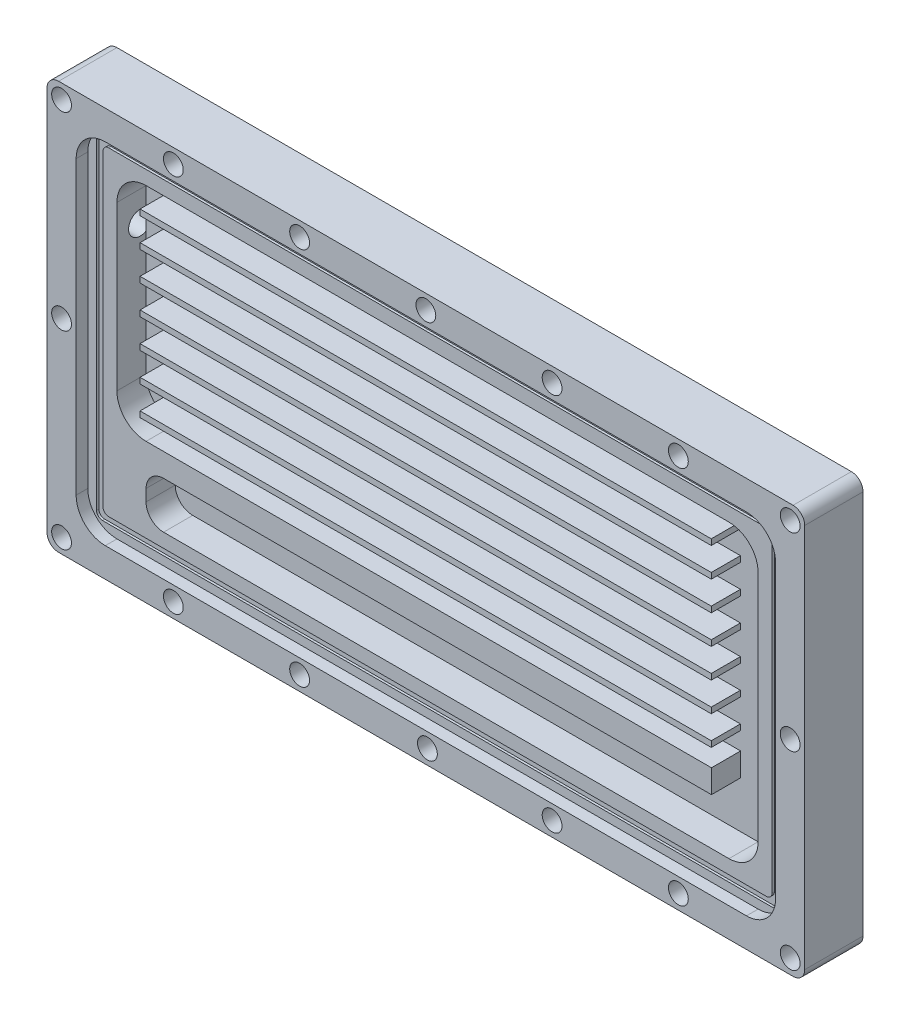
SolidWorks part; units mm, degrees
ref_plane "Plan de face" through (0, 0, 0) normal (0, 0, 1) x (1, 0, 0)
ref_plane "Plan de dessus" through (0, 0, 0) normal (0, 1, 0) x (1, 0, 0)
ref_plane "Plan de droite" through (0, 0, 0) normal (1, 0, 0) x (0, 0, -1)
sketch "Esquisse1" plane through (0, 0, 0) normal (0, 0, 1) x (1, 0, 0)
  line L1 (2, 0) -> (128, 0)
  line L2 (0, 2) -> (0, 68)
  line L3 (2, 70) -> (128, 70)
  line L4 (130, 2) -> (130, 68)
  arc A0 (2, 0) -> (0, 2) centre (2, 2) cw
  arc A1 (128, 0) -> (130, 2) centre (128, 2) ccw
  arc A2 (128, 70) -> (130, 68) centre (128, 68) cw
  arc A3 (0, 68) -> (2, 70) centre (2, 68) cw
  point P7 (0, 0)
  point P10 (130, 0)
  point P15 (0, 70)
  dimension "D3" = 2
  dimension "D1" = 130
  dimension "D2" = 70
extrude "Boss.-Extru.1" add sketch "Esquisse1" along normal blind 10
sketch "Esquisse18" plane through (0, 0, 10) normal (0, 0, 1) x (1, 0, 0)
  line L0 (128, 70) -> (2, 70) construction
  line L1 (10, 5) -> (120, 5)
  line L2 (5, 10) -> (5, 60)
  line L3 (10, 65) -> (120, 65)
  line L4 (125, 10) -> (125, 60)
  line L5 (130, 2) -> (130, 68) construction
  line L6 (0, 68) -> (0, 2) construction
  line L7 (2, 0) -> (128, 0) construction
  arc A0 (120, 65) -> (125, 60) centre (120, 60) cw
  arc A1 (120, 5) -> (125, 10) centre (120, 10) ccw
  arc A2 (10, 5) -> (5, 10) centre (10, 10) cw
  arc A3 (5, 60) -> (10, 65) centre (10, 60) cw
  dimension "D5" = 5
  dimension "D1" = 5
  dimension "D2" = 5
  dimension "D3" = 5
  dimension "D4" = 5
extrude "Enlèv. mat.-Extru.1" cut sketch "Esquisse18" against normal blind 2
sketch "Esquisse19" plane through (0, 0, 0) normal (-1, 0, 0) x (0, 0, 1)
  circle A0 centre (4, 50) radius 2
  circle A1 centre (4, 12) radius 2
sketch "Esquisse20" plane through (0, 0, 8) normal (0, 0, 1) x (1, 0, 0)
  line L0 (15, 60) -> (115, 60)
  line L9 (120, 55) -> (120, 15)
  line L10 (115, 10) -> (18, 10)
  line L12 (18, 18) -> (112, 18)
  line L14 (112, 22) -> (15, 22)
  line L25 (112, 18) -> (112, 22)
  line L26 (10, 27) -> (10, 55)
  line L28 (15, 13) -> (15, 15)
  line L32 (5, 60) -> (5, 10) construction
  line L33 (5, 60) -> (5, 10) construction
  line L34 (10, 5) -> (120, 5) construction
  line L35 (125, 10) -> (125, 60) construction
  line L36 (120, 65) -> (10, 65) construction
  arc A0 (15, 22) -> (10, 27) centre (15, 27) cw
  arc A1 (10, 55) -> (15, 60) centre (15, 55) cw
  arc A2 (120, 15) -> (115, 10) centre (115, 15) cw
  arc A3 (115, 60) -> (120, 55) centre (115, 55) cw
  arc A4 (15, 15) -> (18, 18) centre (18, 15) cw
  arc A5 (18, 10) -> (15, 13) centre (18, 13) cw
  dimension "D10" = 5
  dimension "D9" = 3
  dimension "D11" = 3
  dimension "D2" = 5
  dimension "D3" = 10
  dimension "D4" = 8
  dimension "D5" = 8
  dimension "D6" = 5
  dimension "D7" = 5
  dimension "D8" = 5
  dimension "D14" = 4
extrude "Enlèv. mat.-Extru.3" cut sketch "Esquisse20" against normal blind 5
sketch "Esquisse23" plane through (0, 0, 3) normal (0, 0, 1) x (1, 0, 0)
  line L1 (13.9661, 56) -> (111.9661, 56)
  line L2 (13.9661, 56) -> (13.9661, 55)
  line L3 (13.9661, 55) -> (111.9661, 55)
  line L4 (111.9661, 56) -> (111.9661, 55)
  line L28 (115, 60) -> (15, 60) construction
  line L29 (13.9661, 51) -> (111.9661, 51)
  line L30 (13.9661, 50) -> (111.9661, 50)
  line L31 (111.9661, 51) -> (111.9661, 50)
  line L32 (13.9661, 51) -> (13.9661, 50)
  line L33 (13.9661, 46) -> (111.9661, 46)
  line L34 (13.9661, 45) -> (111.9661, 45)
  line L35 (111.9661, 46) -> (111.9661, 45)
  line L36 (13.9661, 46) -> (13.9661, 45)
  line L37 (13.9661, 41) -> (111.9661, 41)
  line L38 (13.9661, 40) -> (111.9661, 40)
  line L39 (111.9661, 41) -> (111.9661, 40)
  line L40 (13.9661, 41) -> (13.9661, 40)
  line L41 (13.9661, 36) -> (111.9661, 36)
  line L42 (13.9661, 35) -> (111.9661, 35)
  line L43 (111.9661, 36) -> (111.9661, 35)
  line L44 (13.9661, 36) -> (13.9661, 35)
  line L45 (13.9661, 31) -> (111.9661, 31)
  line L46 (13.9661, 30) -> (111.9661, 30)
  line L47 (111.9661, 31) -> (111.9661, 30)
  line L48 (13.9661, 31) -> (13.9661, 30)
  line L49 (13.9661, 26) -> (111.9661, 26)
  line L50 (13.9661, 25) -> (111.9661, 25)
  line L51 (111.9661, 26) -> (111.9661, 25)
  line L52 (13.9661, 26) -> (13.9661, 25)
  dimension "D1" = 98
  dimension "D2" = 7
  dimension "D3" = 1
  dimension "D4" = 4
extrude "Boss.-Extru.2" add sketch "Esquisse23" along normal blind 5
sketch "Esquisse24" plane through (0, 0, 8) normal (0, 0, 1) x (1, 0, 0)
  line L0 (8.6, 62.4) -> (121.4, 62.4)
  line L2 (6.5, 62.5) -> (6.5, 7.5)
  line L3 (7.5, 6.5) -> (7.9673, 6.5)
  line L5 (7.9673, 6.5) -> (122.5, 6.5)
  line L10 (123.5, 7.5) -> (123.5, 62.5)
  line L12 (122.4, 8.6) -> (122.4, 61.4)
  line L15 (122.5, 63.5) -> (7.5, 63.5)
  line L17 (121.4, 7.6) -> (8.6, 7.6)
  line L18 (7.6, 8.6) -> (7.6, 61.4)
  line L19 (5, 60) -> (5, 10) construction
  line L20 (120, 65) -> (10, 65) construction
  line L21 (125, 10) -> (125, 60) construction
  line L22 (10, 5) -> (120, 5) construction
  arc A0 (121.4, 7.6) -> (122.4, 8.6) centre (121.4, 8.6) ccw
  arc A1 (122.5, 6.5) -> (123.5, 7.5) centre (122.5, 7.5) ccw
  arc A2 (123.5, 62.5) -> (122.5, 63.5) centre (122.5, 62.5) ccw
  arc A3 (121.4, 62.4) -> (122.4, 61.4) centre (121.4, 61.4) cw
  arc A4 (8.6, 62.4) -> (7.6, 61.4) centre (8.6, 61.4) ccw
  arc A5 (7.5, 63.5) -> (6.5, 62.5) centre (7.5, 62.5) ccw
  arc A6 (6.5, 7.5) -> (7.5, 6.5) centre (7.5, 7.5) ccw
  arc A7 (8.6, 7.6) -> (7.6, 8.6) centre (8.6, 8.6) cw
  dimension "D9" = 1
  dimension "D1" = 1.1
  dimension "D2" = 1.1
  dimension "D3" = 1.5
  dimension "D4" = 1.5
  dimension "D5" = 1.5
  dimension "D6" = 1.1
  dimension "D7" = 1.1
  dimension "D8" = 1.5
extrude "Enlèv. mat.-Extru.4" cut sketch "Esquisse24" against normal blind 0.4
extrude "Enlèv. mat.-Extru.5" cut sketch "Esquisse19" against normal blind 10
sketch "Esquisse25" plane through (0, 0, 10) normal (0, 0, 1) x (1, 0, 0)
  line L0 (65, 76.2778) -> (65, -9.8597) construction
  line L1 (86.66, 74.4744) -> (86.66, -13.393) construction
  line L2 (108.32, 74.4744) -> (108.32, -15.3804) construction
  line L3 (43.34, 74.4744) -> (43.34, -9.8597) construction
  line L4 (21.68, 74.4744) -> (21.68, -9.8597) construction
  line L5 (-6.6333, 67.5) -> (135.9663, 67.5) construction
  line L6 (-6.6333, 35) -> (142.1485, 35) construction
  line L7 (2, 0) -> (128, 0) construction
  line L8 (-6.6333, 2.5) -> (137.1669, 2.5) construction
  line L9 (130, 2) -> (130, 68) construction
  line L10 (128, 70) -> (2, 70) construction
  line L11 (2.5, 74.4744) -> (2.5, -9.8597) construction
  line L12 (127.5, 74.4744) -> (127.5, -3.6286) construction
  line L13 (0, 68) -> (0, 2) construction
  dimension "D1" = 2.5
  dimension "D2" = 35
  dimension "D3" = 65
  dimension "D4" = 21.66
  dimension "D5" = 21.66
  dimension "D6" = 21.66
  dimension "D7" = 21.66
  dimension "D8" = 2.5
  dimension "D9" = 2.5
  dimension "D10" = 2.5
hole_wizard "Dégagement M31" positions "Esquisse26" profile "Esquisse27" hole size "M3" standard "ISO"
sketch "Esquisse26" plane through (0, 0, 10) normal (0, 0, 1) x (1, 0, 0)
  line L0 (-6.6333, 67.5) -> (135.9663, 67.5) construction
  line L1 (127.5, 74.4744) -> (127.5, -3.6286) construction
  line L2 (108.32, 74.4744) -> (108.32, -15.3804) construction
  line L3 (86.66, 74.4744) -> (86.66, -13.393) construction
  line L4 (65, 76.2778) -> (65, -9.8597) construction
  line L5 (43.34, 74.4744) -> (43.34, -9.8597) construction
  line L6 (21.68, 74.4744) -> (21.68, -9.8597) construction
  line L7 (2.5, 74.4744) -> (2.5, -9.8597) construction
  line L8 (-6.6333, 35) -> (142.1485, 35) construction
  line L9 (-6.6333, 2.5) -> (137.1669, 2.5) construction
  point P0 (127.5, 67.5)
  point P6 (108.32, 67.5)
  point P10 (86.66, 67.5)
  point P14 (65, 67.5)
  point P18 (43.34, 67.5)
  point P22 (21.68, 67.5)
  point P26 (2.5, 67.5)
  point P30 (2.5, 35)
  point P34 (2.5, 2.5)
  point P38 (21.68, 2.5)
  point P40 (43.34, 2.5)
  point P42 (65.2668, 2.5)
  point P44 (86.66, 2.5)
  point P46 (108.32, 2.5)
  point P48 (127.5, 2.5)
  point P50 (127.5, 35)
sketch "Esquisse27" plane through (127.5, 67.5, 10) normal (1, 0, 0) x (0, -1, 0)
  line L0 (0, 0) -> (0, 5)
  line L1 (0, 5) -> (1.7, 3.9785)
  line L2 (1.7, 3.9785) -> (1.7, 0)
  line L5 (1.7, 0) -> (0, 0)
  line L10 (0, 5) -> (-1.7, 3.9785) construction
  line L11 (0, -6.35) -> (0, 107.95) construction
  dimension "Diamètre du perçage" = 3.4
  dimension "Profondeur du perçage" = 5
  dimension "Angle de pointe" = 118
